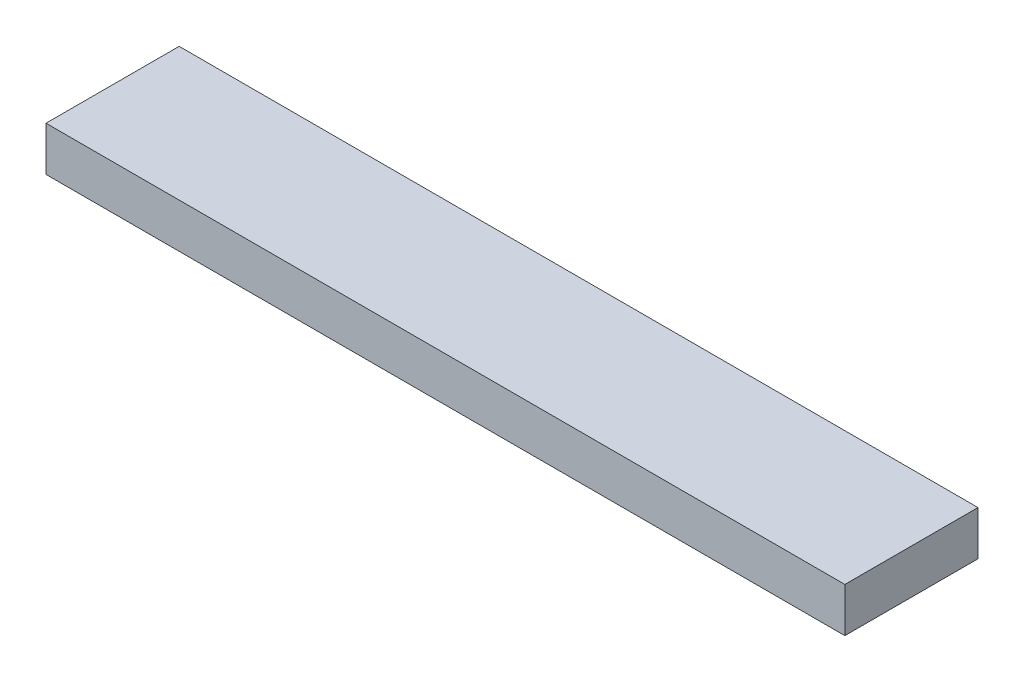
SolidWorks part; units mm, degrees
ref_plane "Front Plane" through (0, 0, 0) normal (0, 0, 1) x (1, 0, 0)
ref_plane "Top Plane" through (0, 0, 0) normal (0, 1, 0) x (1, 0, 0)
ref_plane "Right Plane" through (0, 0, 0) normal (1, 0, 0) x (0, 0, -1)
sketch "Sketch1" plane through (0, 0, 0) normal (0, 1, 0) x (1, 0, 0)
  line L1 (-90, -15) -> (90, -15)
  line L2 (-90, -15) -> (-90, 15)
  line L3 (-90, 15) -> (90, 15)
  line L4 (90, -15) -> (90, 15)
  line L5 (-90, -15) -> (90, 15) construction
  line L6 (-90, 15) -> (90, -15) construction
  point P0 (0, 0)
  dimension "D1" = 180
  dimension "D2" = 30
extrude "Boss-Extrude1" add sketch "Sketch1" along normal blind 10
